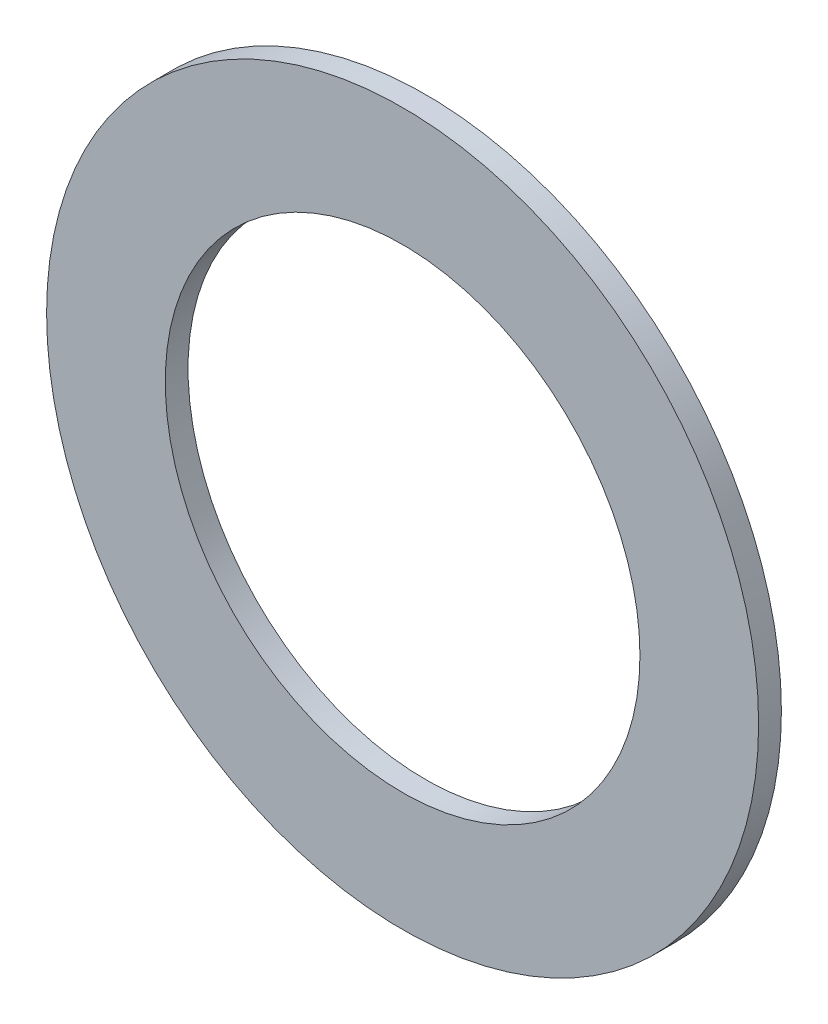
SolidWorks part; units mm, degrees
material "Brass"
ref_plane "Front Plane" through (0, 0, 0) normal (0, 0, 1) x (1, 0, 0)
ref_plane "Top Plane" through (0, 0, 0) normal (0, 1, 0) x (1, 0, 0)
ref_plane "Right Plane" through (0, 0, 0) normal (1, 0, 0) x (0, 0, -1)
sketch "Sketch1" plane through (0, 0, 0) normal (0, 0, 1) x (1, 0, 0)
  circle A0 centre (0, 0) radius 3.175
  circle A1 centre (0, 0) radius 4.7625
  dimension "D1" = 6.35
  dimension "D2" = 9.525
extrude "Boss-Extrude1" add sketch "Sketch1" along normal blind 0.3048
